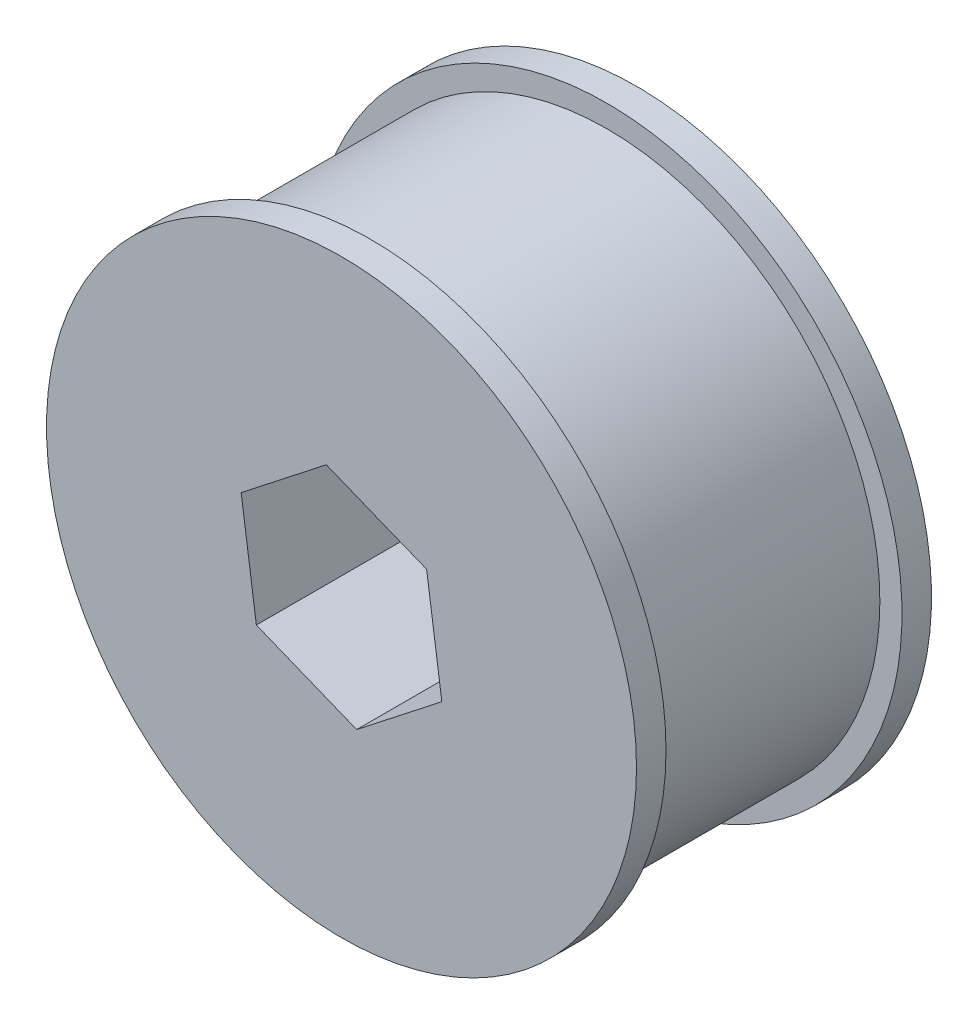
SolidWorks part; units mm, degrees
ref_plane "Front Plane" through (0, 0, 0) normal (0, 0, 1) x (1, 0, 0)
ref_plane "Top Plane" through (0, 0, 0) normal (0, 1, 0) x (1, 0, 0)
ref_plane "Right Plane" through (0, 0, 0) normal (1, 0, 0) x (0, 0, -1)
sketch "Sketch1" plane through (0, 0, 0) normal (0, 0, 1) x (1, 0, 0)
  circle A0 centre (0, 0) radius 18.5
  dimension "D1" = 37
extrude "Boss-Extrude1" add sketch "Sketch1" along normal blind 20
sketch "Sketch2" plane through (0, 0, 20) normal (0, 0, 1) x (1, 0, 0)
  circle A0 centre (0, 0) radius 20
  dimension "D1" = 40
extrude "Boss-Extrude2" add sketch "Sketch2" against normal blind 2 contours A0
sketch "Sketch3" plane through (0, 0, 0) normal (0, 0, -1) x (-1, 0, 0)
  circle A0 centre (0, 0) radius 20
  dimension "D1" = 40
extrude "Boss-Extrude3" add sketch "Sketch3" against normal blind 2
sketch "Sketch4" plane through (0, 0, 20) normal (0, 0, 1) x (1, 0, 0)
  line L1 (5.7722, 4.5216) -> (-1.0297, 7.2597)
  line L2 (-1.0297, 7.2597) -> (-6.8019, 2.7381)
  line L3 (-6.8019, 2.7381) -> (-5.7722, -4.5216)
  line L4 (-5.7722, -4.5216) -> (1.0297, -7.2597)
  line L5 (1.0297, -7.2597) -> (6.8019, -2.7381)
  line L6 (6.8019, -2.7381) -> (5.7722, 4.5216)
  circle A0 centre (0, 0) radius 6.35 construction
  dimension "D1" = 12.7
extrude "Cut-Extrude1" cut sketch "Sketch4" against normal through all
